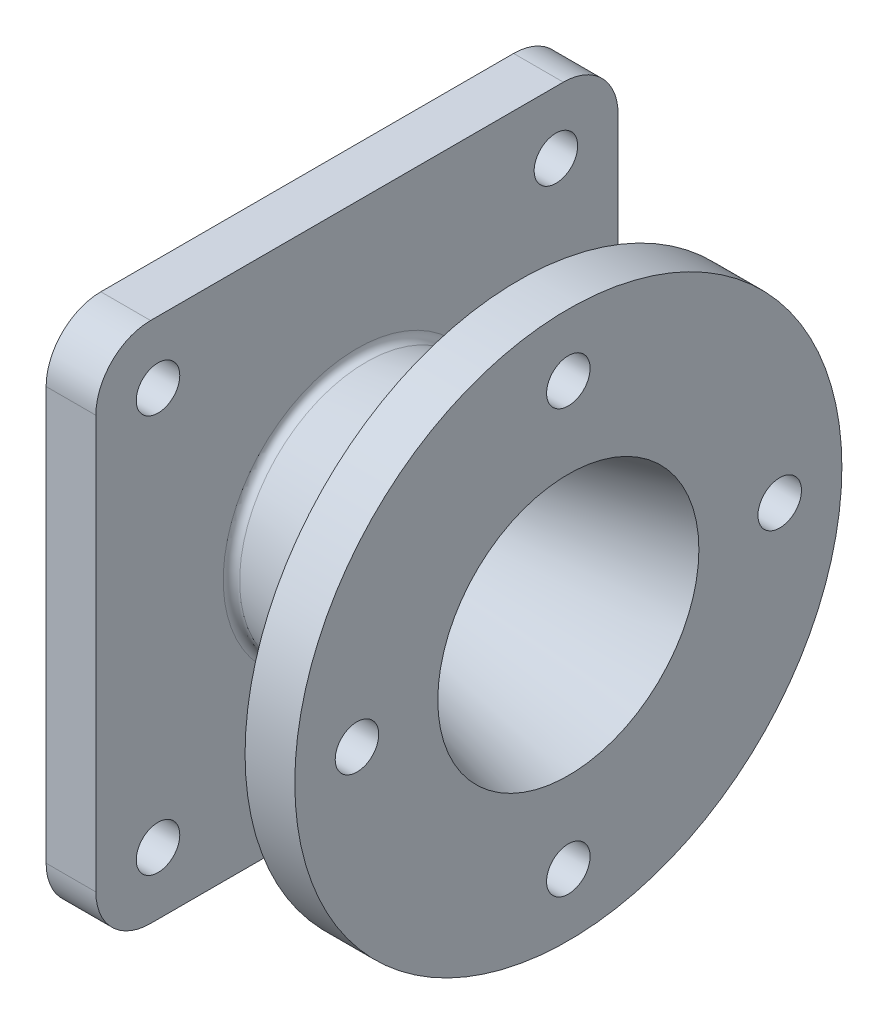
SolidWorks part; units mm, degrees
material "Сталь"
ref_plane "Спереди" through (0, 0, 0) normal (0, 0, 1) x (1, 0, 0)
ref_plane "Сверху" through (0, 0, 0) normal (0, 1, 0) x (1, 0, 0)
ref_plane "Справа" through (0, 0, 0) normal (1, 0, 0) x (0, 0, -1)
sketch "Эскиз1" plane through (0, 0, 0) normal (0, 0, 1) x (1, 0, 0)
  line L0 (0, 0) -> (-243.1706, 0) construction
  line L1 (0, 52.5) -> (0, 110)
  line L2 (0, 110) -> (-20, 110)
  line L3 (-20, 110) -> (-20, 65)
  line L4 (-85, 50) -> (-20, 65)
  line L5 (-105, 35) -> (-113, 35)
  line L6 (-85, 50) -> (-85, 105)
  line L7 (-85, 105) -> (-105, 105)
  line L8 (-105, 105) -> (-105, 62.5)
  line L9 (-105, 62.5) -> (-130, 62.5)
  line L10 (-130, 62.5) -> (-130, 28.7125)
  line L11 (-113, 35) -> (-113, 28.7125)
  line L12 (0, 52.5) -> (-105, 25)
  line L13 (-105, 25) -> (-105, 35)
  line L14 (-113, 28.7125) -> (-130, 28.7125)
  dimension "D1" = 220
  dimension "D2" = 20
  dimension "D3" = 105
  dimension "D4" = 100
  dimension "D5" = 130
  dimension "D6" = 65
  dimension "D7" = 25
  dimension "D8" = 210
  dimension "D9" = 105
  dimension "D10" = 125
  dimension "D11" = 70
  dimension "D12" = 50
  dimension "D13" = 57.425
  dimension "D14" = 8
revolve "Повернуть1" add sketch "Эскиз1" angle 360 about L0
cosmetic thread "Условное изображение резьбы1" parameters "D2"=64
sketch "Эскиз2" plane through (0, 0, 0) normal (1, 0, 0) x (0, 0, -1)
  circle A0 centre (0, 85) radius 8.75
  dimension "D2" = 17.5
  dimension "D1" = 85
extrude "Вырез-Вытянуть1" cut sketch "Эскиз2" against normal up to next (20 mm away)
pattern_circular "Круговой массив1" count 4 over 360 about axis through (0, 0, 0) along (1, 0, 0) of "Вырез-Вытянуть1"
sketch "Эскиз3" plane through (-105, 0, 0) normal (-1, 0, 0) x (0, 0, 1)
  line L1 (-105, -105) -> (105, -105)
  line L2 (-105, -105) -> (-105, 105)
  line L3 (-105, 105) -> (105, 105)
  line L4 (105, -105) -> (105, 105)
  line L5 (-105, -105) -> (105, 105) construction
  line L6 (-105, 105) -> (105, -105) construction
  circle A4 centre (0, 0) radius 105 construction
  circle A5 centre (0, 0) radius 35 construction
  circle A6 centre (0, 0) radius 35
  point P0 (0, 0)
extrude "Бобышка-Вытянуть1" add sketch "Эскиз3" against normal up to surface (20 mm away) up to face at (-85, 0, -105)
sketch "Эскиз4" plane through (-105, 0, 0) normal (-1, 0, 0) x (0, 0, 1)
  line L0 (0, 0) -> (105, 105) construction
  circle A0 centre (80, 80) radius 8.75
  dimension "D1" = 80
  dimension "D2" = 17.5
extrude "Вырез-Вытянуть2" cut sketch "Эскиз4" against normal up to surface (20 mm away)
fillet "Скругление1" radius 22 4 edges at (-95, 105, -105) (-95, -105, -105) (-95, -105, 105) (-95, 105, 105)
pattern_circular "Круговой массив5" count 4 over 360 about axis through (0, 0, 0) along (1, 0, 0) of "Вырез-Вытянуть2"
chamfer "Фаска1" distance 3.2875 angle 45 1 edges at (-130, 0, -28.7125)
fillet "Скругление2" radius 3 2 edges at (-20, 0, -65) (-85, 0, -50)
